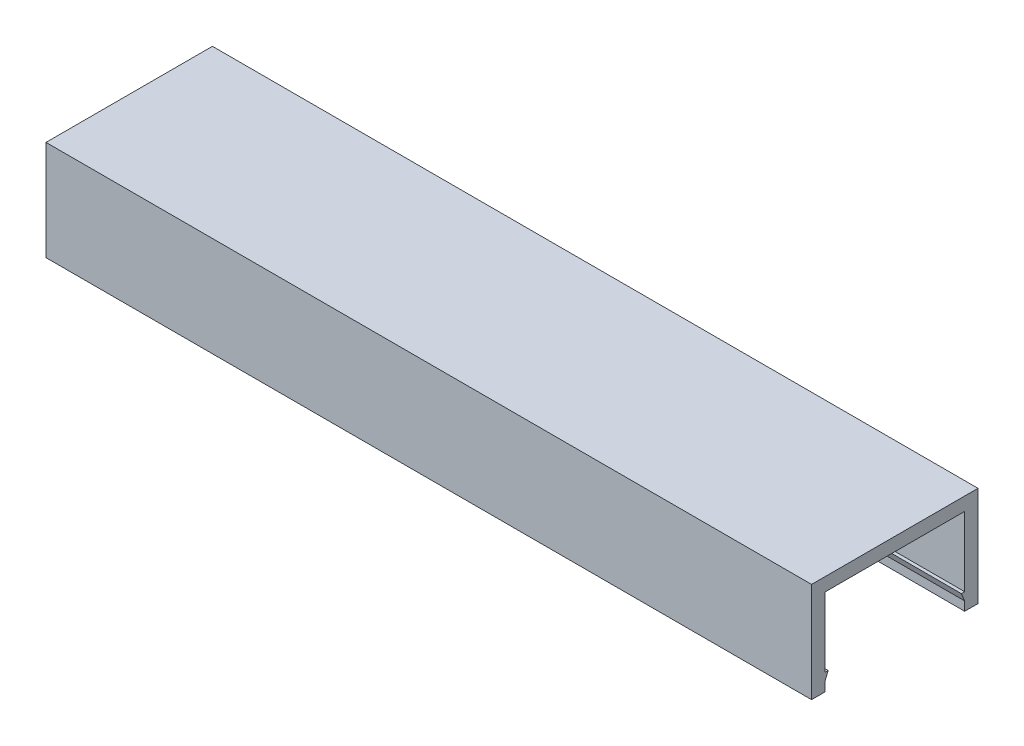
SolidWorks part; units mm, degrees
ref_plane "Front Plane" through (0, 0, 0) normal (0, 0, 1) x (1, 0, 0)
ref_plane "Top Plane" through (0, 0, 0) normal (0, 1, 0) x (1, 0, 0)
ref_plane "Right Plane" through (0, 0, 0) normal (1, 0, 0) x (0, 0, -1)
sketch "Croquis1" plane through (0, 0, 0) normal (0, 1, 0) x (1, 0, 0)
  line L0 (-57.5, -12.5) -> (-57.5, 12.5)
  line L1 (-57.5, -12.5) -> (57.5, -12.5)
  line L2 (-57.5, 12.5) -> (57.5, 12.5)
  line L3 (57.5, -12.5) -> (57.5, 12.5)
  line L4 (-57.5, -12.5) -> (57.5, 12.5) construction
  line L5 (-57.5, 12.5) -> (57.5, -12.5) construction
  line L6 (71, -10.35) -> (71, 10.35)
  line L7 (71, -10.35) -> (-71, -10.35)
  line L8 (71, 10.35) -> (-71, 10.35)
  line L9 (-71, -10.35) -> (-71, 10.35)
  line L10 (71, -10.35) -> (-71, 10.35) construction
  line L11 (71, 10.35) -> (-71, -10.35) construction
  point P1 (0, 0)
  point P2 (0, 0)
  dimension "D1" = 115
  dimension "D2" = 25
  dimension "D3" = 142
  dimension "D4" = 2.15
extrude "Saliente-Extruir1" add sketch "Croquis1" along normal blind 15 contours L3 L8 L0 L7 | L8 L3 L2 L0 | L3 L7 L0 L1
sketch "Croquis2" plane through (-57.5, 0, 0) normal (-1, 0, 0) x (0, 0, 1)
  line L0 (-10.5, 13) -> (-10.5, 0)
  line L1 (-10.5, 13) -> (10.5, 13)
  line L2 (-10.5, 0) -> (10.5, 0)
  line L3 (10.5, 13) -> (10.5, 0)
  line L4 (-10.5, 13) -> (10.5, 0) construction
  line L5 (-10.5, 0) -> (10.5, 13) construction
  line L6 (-12.5, 15) -> (-12.5, 0) construction
  line L11 (12.5, 15) -> (-12.5, 15) construction
  line L13 (12.5, 0) -> (-12.5, 0) construction
  line L14 (12.5, 15) -> (12.5, 0) construction
  point P1 (0, 6.5)
  dimension "D1" = 2
  dimension "D2" = 2
  dimension "D3" = 2
  dimension "D4" = 6.5
extrude "Cortar-Extruir1" cut sketch "Croquis2" against normal blind 230
sketch "Croquis11" plane through (-57.5, 0, 0) normal (-1, 0, 0) x (0, 0, 1)
  line L0 (-10.5, 1.35) -> (-10.5, 2.55)
  line L1 (-10.5, 0) -> (-12.5, 0) construction
  line L2 (-10.5, 13) -> (-10.5, 0) construction
  line L3 (-10.5, 2.55) -> (-10, 2.55)
  line L4 (-10, 2.55) -> (-10.5, 1.35)
  line L6 (0, 0) -> (0, 8.3198) construction
  line L11 (10.5, 13) -> (-10.5, 13) construction
  line L13 (10, 2.55) -> (10.5, 1.35)
  line L14 (10.5, 2.55) -> (10, 2.55)
  line L15 (10.5, 1.35) -> (10.5, 2.55)
  dimension "D1" = 10.45
  dimension "D2" = 1.35
  dimension "D3" = 0.5
extrude "Saliente-Extruir4" add sketch "Croquis11" against normal up to surface (115 mm away) up to face at (57.5, 7, 0)
